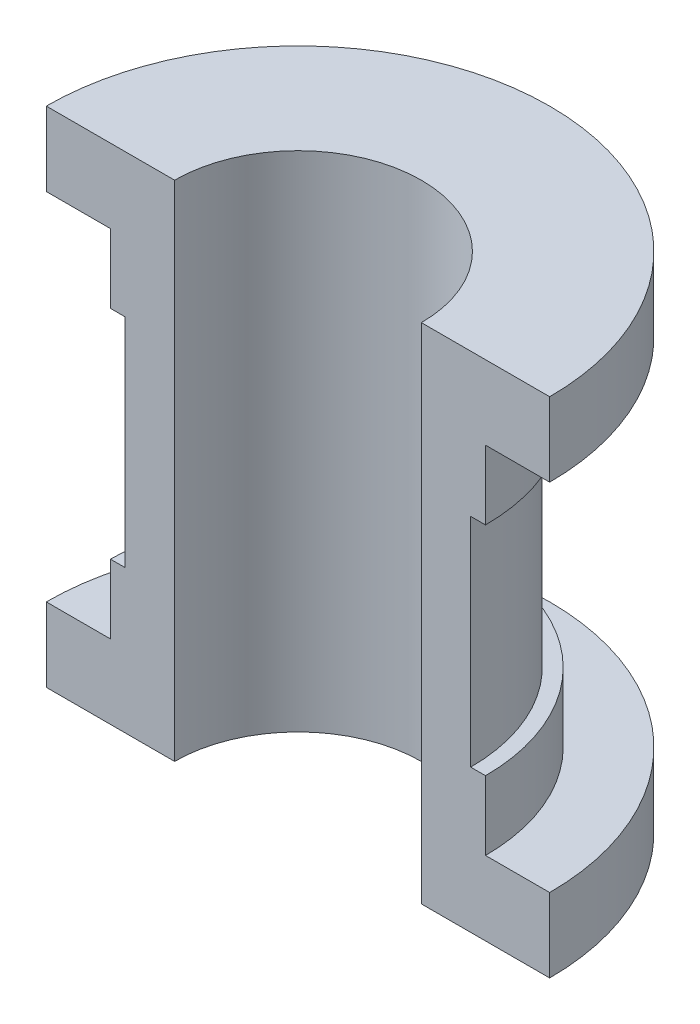
SolidWorks part; units mm, degrees
ref_plane "Front Plane" through (0, 0, 0) normal (0, 0, 1) x (1, 0, 0)
ref_plane "Top Plane" through (0, 0, 0) normal (0, 1, 0) x (1, 0, 0)
ref_plane "Right Plane" through (0, 0, 0) normal (1, 0, 0) x (0, 0, -1)
sketch "Sketch3" plane through (0, 0, 0) normal (0, 0, 1) x (1, 0, 0)
  line L0 (0, 0) -> (0, 128.1875) construction
  line L1 (0, 0) -> (25.5, 0)
  line L2 (25.5, 0) -> (25.5, 7.5)
  line L3 (25.5, 7.5) -> (19, 7.5)
  line L4 (19, 7.5) -> (19, 14.5)
  line L5 (19, 14.5) -> (17.5, 14.5)
  line L6 (17.5, 14.5) -> (17.5, 36.5)
  line L7 (17.5, 36.5) -> (19, 36.5)
  line L8 (19, 36.5) -> (19, 43.5)
  line L9 (19, 43.5) -> (25.5, 43.5)
  line L10 (25.5, 43.5) -> (25.5, 51)
  line L11 (25.5, 51) -> (0, 51)
  line L12 (0, 51) -> (0, 0)
  dimension "D1" = 51
  dimension "D2" = 22
  dimension "D3" = 36
  dimension "D4" = 51
  dimension "D5" = 38
  dimension "D6" = 35
revolve "Revolve1" add sketch "Sketch3" angle 180 about L0
sketch "Sketch4" plane through (0, 51, 0) normal (0, 1, 0) x (1, 0, 0)
  line L0 (-25.5, 0) -> (25.5, 0) construction
  line L1 (-12.5, 0) -> (12.5, 0)
  arc A0 (12.5, 0) -> (-12.5, 0) centre (0, 0) ccw
  dimension "D1" = 25
extrude "Cut-Extrude1" cut sketch "Sketch4" against normal through all
ref_plane "Plane1" through (0, 0, -23.5) normal (0, 0, -1) x (-1, 0, 0)
sketch "Sketch7" plane through (0, 0, -23.5) normal (0, 0, -1) x (-1, 0, 0)
  line L0 (-19, 36.5) -> (19, 36.5) construction
  line L1 (-25.5, 0) -> (25.5, 0) construction
  circle A0 centre (0, 25.5) radius 3
  point P2 (0, 36.5)
  dimension "D1" = 6
  dimension "D2" = 25.5
extrude "Boss-Extrude1" add sketch "Sketch7" against normal up to surface (11.3653 mm away)
